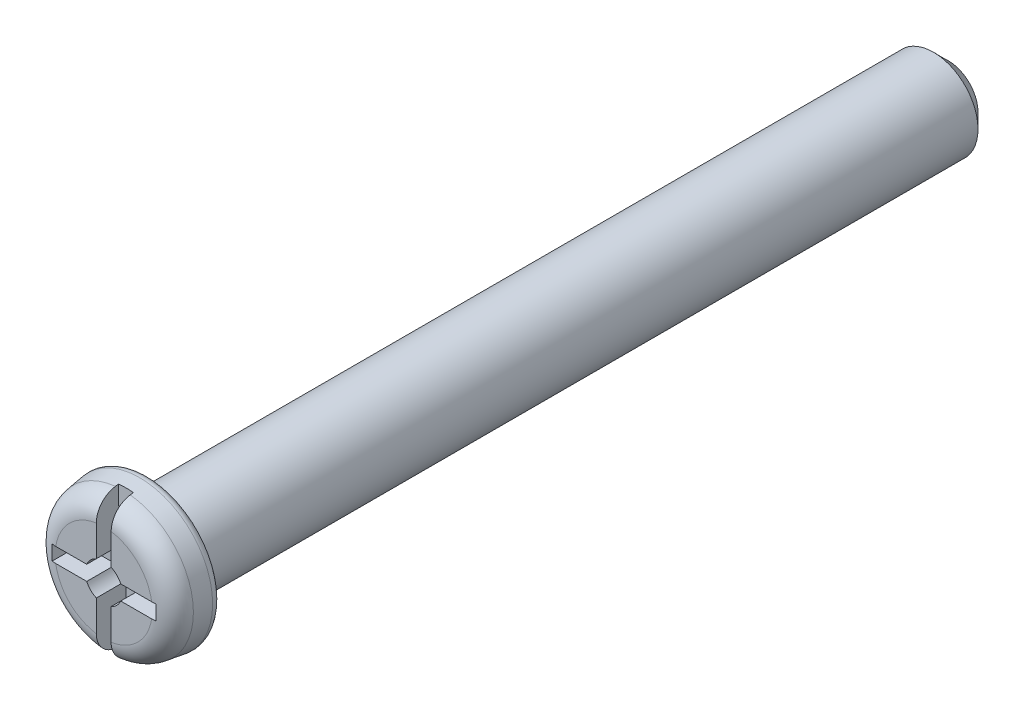
SolidWorks part; units mm, degrees
ref_plane "Plane1" through (0, 0, 0) normal (0, 0, 1) x (1, 0, 0)
ref_plane "Plane2" through (0, 0, 0) normal (0, 1, 0) x (1, 0, 0)
ref_plane "Plane3" through (0, 0, 0) normal (1, 0, 0) x (0, 0, -1)
sketch "Esquisse1" plane through (0, 0, 0) normal (0, 0, 1) x (1, 0, 0)
  circle A0 centre (0, 0) radius 2.5
  dimension "D1" = 5
extrude "Base-Extrusion" add sketch "Esquisse1" along normal blind 1.5 draft 8
fillet "Congé1" radius 0.75
fillet "Congé2" radius 0.25
sketch "Esquisse2" plane through (0, 0, 0) normal (0, 0, -1) x (-1, 0, 0)
  circle A0 centre (0, 0) radius 1.5
  dimension "D1" = 3
extrude "Boss.-Extru.1" add sketch "Esquisse2" along normal blind 27
chamfer "Chanfrein1" distance 0.5 angle 45
sketch "Esquisse4" plane through (0, 0, 1.5) normal (0, 0, 1) x (1, 0, 0)
  line L0 (0, 0) -> (0, 2) construction
  line L1 (-0.25, 1.75) -> (-0.25, 0.5728)
  line L2 (0.25, 1.75) -> (0.25, 0.5728)
  line L3 (-0.25, 1.75) -> (0.25, 1.75)
  line L4 (1.75, -0.25) -> (0.5728, -0.25)
  line L5 (1.75, 0.25) -> (1.75, -0.25)
  line L6 (1.75, 0.25) -> (0.5728, 0.25)
  line L7 (-0.25, -1.75) -> (-0.25, -0.5728)
  line L8 (0.25, -1.75) -> (-0.25, -1.75)
  line L9 (0.25, -1.75) -> (0.25, -0.5728)
  line L10 (-1.75, 0.25) -> (-0.5728, 0.25)
  line L11 (-1.75, -0.25) -> (-1.75, 0.25)
  line L12 (-1.75, -0.25) -> (-0.5728, -0.25)
  arc A0 (0.5728, 0.25) -> (0.25, 0.5728) centre (0, 0) ccw
  arc A1 (0.25, -0.5728) -> (0.5728, -0.25) centre (0, 0) ccw
  arc A2 (-0.5728, -0.25) -> (-0.25, -0.5728) centre (0, 0) ccw
  arc A3 (-0.25, 0.5728) -> (-0.5728, 0.25) centre (0, 0) ccw
  dimension "D1" = 1.25
  dimension "D2" = 0.5
  dimension "D3" = 1.75
extrude "Enlèv. mat.-Extru.1" cut sketch "Esquisse4" against normal blind 1
sketch "Esquisse5" plane through (0, 0, 1.5) normal (0, 0, 1) x (1, 0, 0)
  line L1 (-0.25, 2.5114) -> (0.25, 2.5114)
  line L2 (-0.25, 2.5114) -> (-0.25, -2.4889)
  line L3 (-0.25, -2.4889) -> (0.25, -2.4889)
  line L4 (0.25, 2.5114) -> (0.25, -2.4889)
extrude "Enlèv. mat.-Extru.2" cut sketch "Esquisse5" against normal blind 0.75
